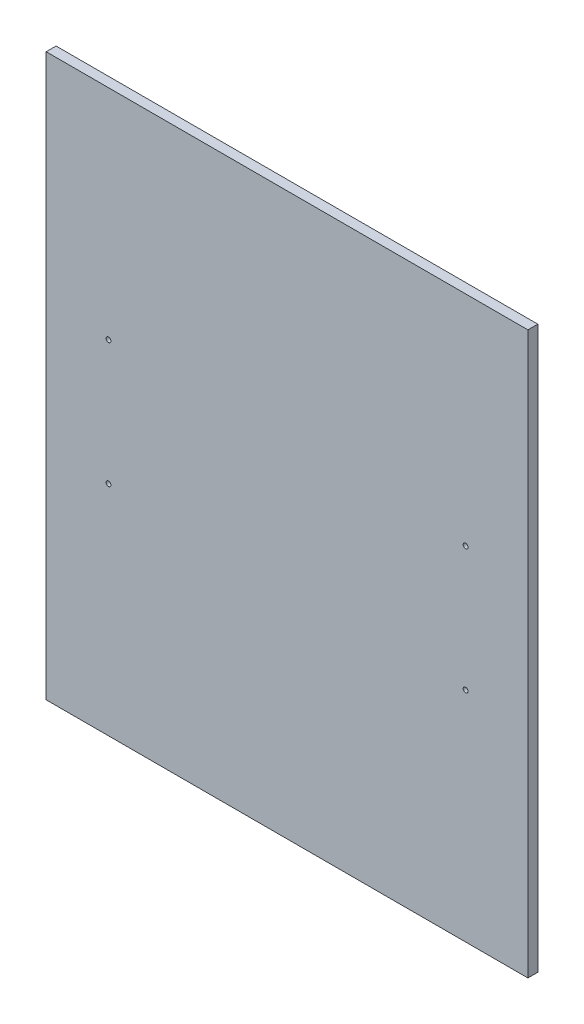
SolidWorks part; units mm, degrees
ref_plane "Front Plane" through (0, 0, 0) normal (0, 0, 1) x (1, 0, 0)
ref_plane "Top Plane" through (0, 0, 0) normal (0, 1, 0) x (1, 0, 0)
ref_plane "Right Plane" through (0, 0, 0) normal (1, 0, 0) x (0, 0, -1)
sketch "Sketch1" plane through (0, 0, 0) normal (0, 0, 1) x (1, 0, 0)
  line L0 (0, 180) -> (309, 180) construction
  line L1 (0, 0) -> (309, 0)
  line L2 (0, 0) -> (0, 360)
  line L3 (0, 360) -> (309, 360)
  line L4 (309, 0) -> (309, 360)
  line L5 (154.5, 180) -> (154.5, 205.7754) construction
  circle A0 centre (40, 220) radius 1.55
  circle A1 centre (40, 140) radius 1.55
  circle A2 centre (269, 140) radius 1.55
  circle A3 centre (269, 220) radius 1.55
  dimension "D3" = 3.1
  dimension "D4" = 40
  dimension "D1" = 360
  dimension "D2" = 309
  dimension "D5" = 40
extrude "Boss-Extrude1" add sketch "Sketch1" along normal blind 6.35
